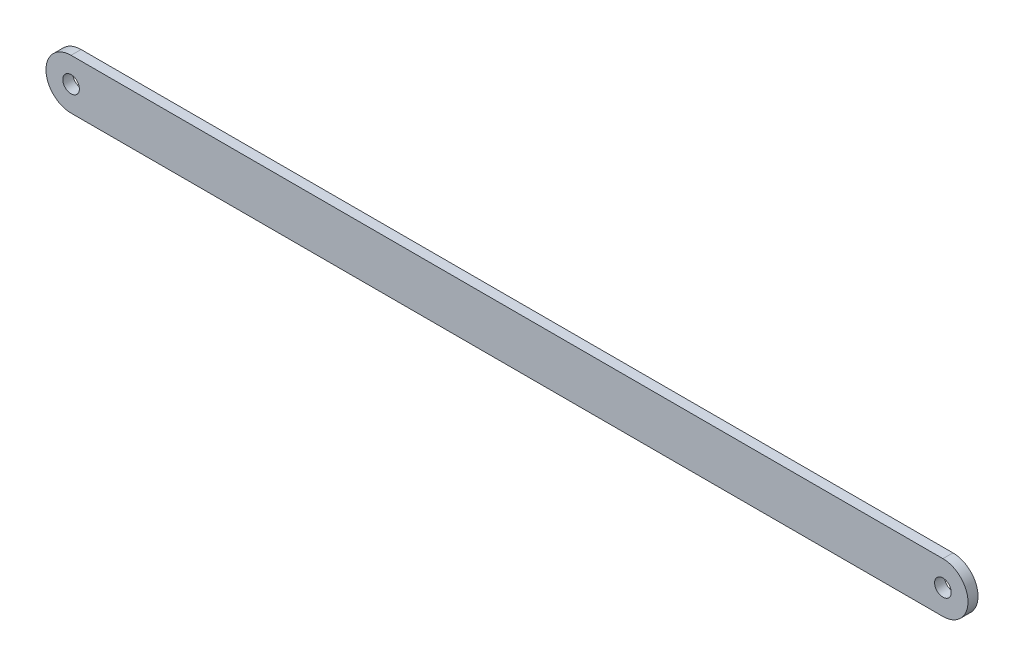
SolidWorks part; units mm, degrees
ref_plane "Přední rovina" through (0, 0, 0) normal (0, 0, 1) x (1, 0, 0)
ref_plane "Horní rovina" through (0, 0, 0) normal (0, 1, 0) x (1, 0, 0)
ref_plane "Pravá rovina" through (0, 0, 0) normal (1, 0, 0) x (0, 0, -1)
sketch "Skica1" plane through (0, 0, 0) normal (0, 0, 1) x (1, 0, 0)
  line L0 (0, 12.5) -> (435, 12.5)
  line L1 (0, -12.5) -> (435, -12.5)
  line L2 (0, 12.5) -> (0, -12.5) construction
  line L3 (435, -12.5) -> (435, 12.5) construction
  line L4 (-12.5, 0) -> (447.5, 0) construction
  arc A0 (0, 12.5) -> (0, -12.5) centre (0, 0) ccw
  arc A1 (435, 12.5) -> (435, -12.5) centre (435, 0) cw
  circle A2 centre (0, 0) radius 4.15
  circle A3 centre (435, 0) radius 4.15
  dimension "D3" = 8.3
  dimension "D4" = 8.3
  dimension "D1" = 25
  dimension "D2" = 435
extrude "Přidat vysunutím1" add sketch "Skica1" along normal blind 5
